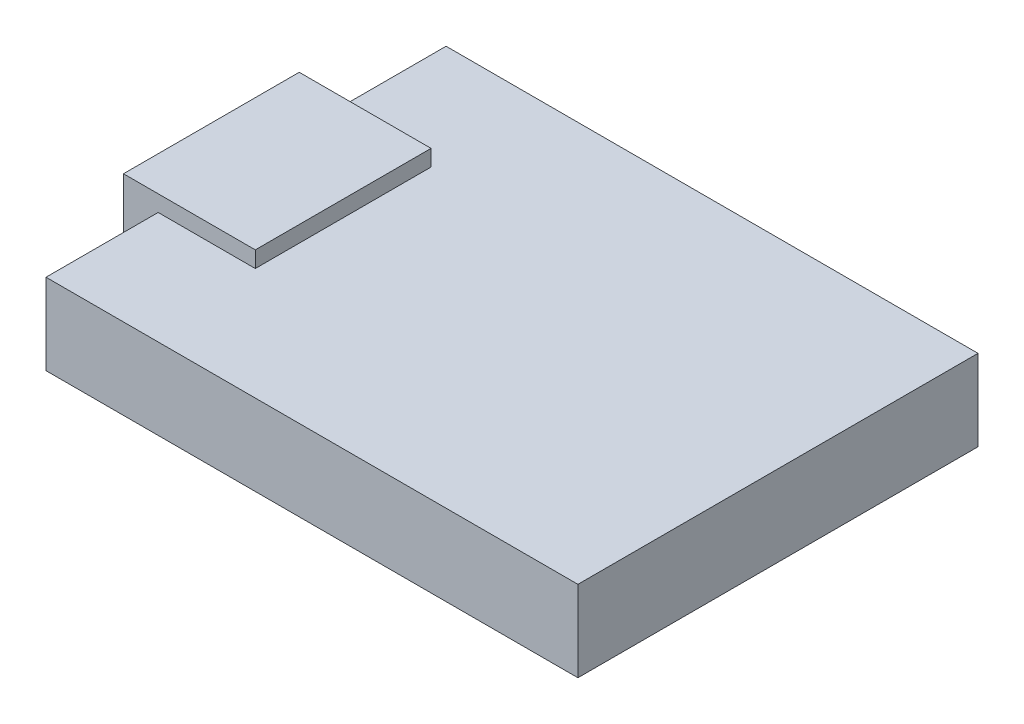
SolidWorks part; units mm, degrees
ref_plane "Спереди" through (0, 0, 0) normal (0, 0, 1) x (1, 0, 0)
ref_plane "Сверху" through (0, 0, 0) normal (0, 1, 0) x (1, 0, 0)
ref_plane "Справа" through (0, 0, 0) normal (1, 0, 0) x (0, 0, -1)
sketch "Эскиз1" plane through (0, 0, 0) normal (0, 1, 0) x (1, 0, 0)
  line L0 (-11.5, 8.65) -> (11.5, 8.65)
  line L1 (-11.5, 8.65) -> (-11.5, -8.65)
  line L2 (11.5, 8.65) -> (11.5, -8.65)
  line L3 (-11.5, -8.65) -> (11.5, -8.65)
  line L4 (-11.5, 8.65) -> (11.5, -8.65) construction
  line L5 (11.5, 8.65) -> (-11.5, -8.65) construction
  point P1 (0, 0)
extrude "Бобышка-Вытянуть1" add sketch "Эскиз1" along normal blind 3.5
sketch "Эскиз2" plane through (0, 3.5, 0) normal (0, 1, 0) x (1, 0, 0)
  line L0 (-11.5, 8.65) -> (-11.5, -8.65) construction
  line L1 (-13, 0) -> (-7.3, 0) construction
  line L2 (-7.2999, 3.8) -> (-7.2999, -3.8)
  line L3 (-7.2999, 3.8) -> (-13.0001, 3.8)
  line L4 (-7.2999, -3.8) -> (-13.0001, -3.8)
  line L5 (-13.0001, 3.8) -> (-13.0001, -3.8)
  line L6 (-7.2999, 3.8) -> (-13.0001, -3.8) construction
  line L7 (-7.2999, -3.8) -> (-13.0001, 3.8) construction
  circle A0 centre (-11.5, 0) radius 3.8 construction
  circle A1 centre (-11.5, 0) radius 1.5 construction
  point P9 (-10.15, 0)
extrude "Бобышка-Вытянуть2" add sketch "Эскиз2" along normal blind 0.7
sketch "Эскиз3" plane through (0, 3.5, 0) normal (0, -1, 0) x (1, 0, 0)
  line L1 (-13.0001, -3.8) -> (-11.5, -3.8)
  line L2 (-13.0001, -3.8) -> (-13.0001, 3.8)
  line L3 (-13.0001, 3.8) -> (-11.5, 3.8)
  line L4 (-11.5, -3.8) -> (-11.5, 3.8)
extrude "Бобышка-Вытянуть3" add sketch "Эскиз3" along normal blind 1.9
